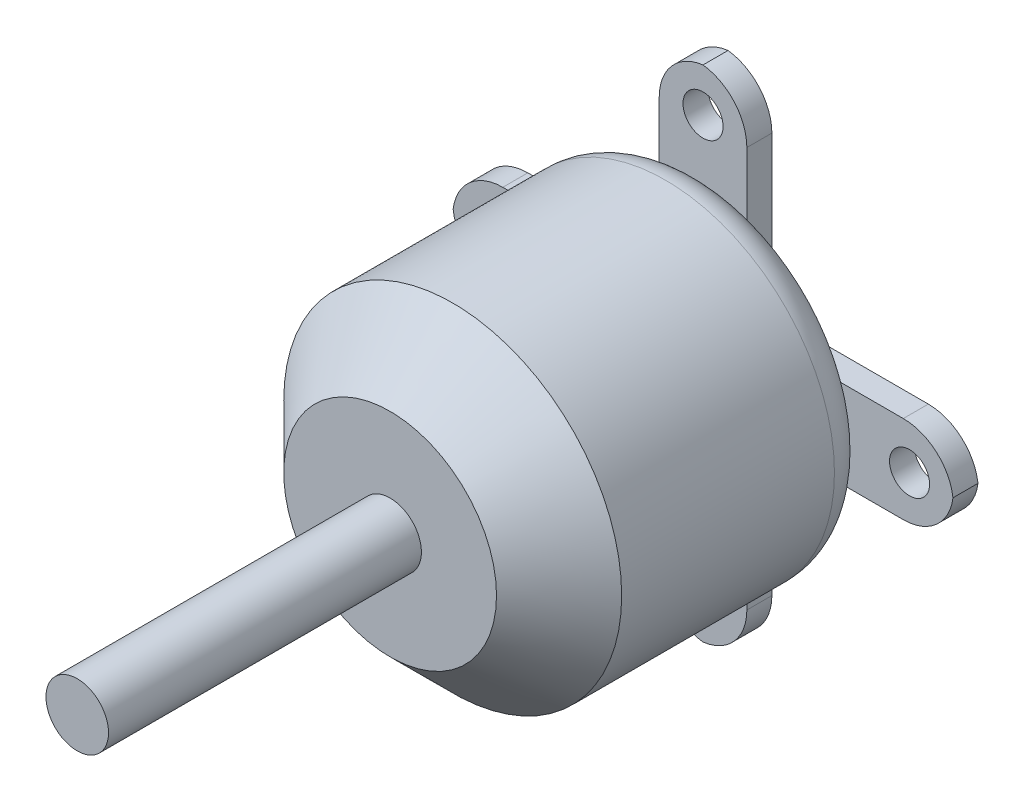
SolidWorks part; units mm, degrees
ref_plane "Front Plane" through (0, 0, 0) normal (0, 0, 1) x (1, 0, 0)
ref_plane "Top Plane" through (0, 0, 0) normal (0, 1, 0) x (1, 0, 0)
ref_plane "Right Plane" through (0, 0, 0) normal (1, 0, 0) x (0, 0, -1)
sketch "Sketch1" plane through (0, 0, 0) normal (0, 0, 1) x (1, 0, 0)
  circle A0 centre (0, 0) radius 13.5
extrude "Boss-Extrude1" add sketch "Sketch1" along normal blind 25
sketch "Sketch2" plane through (0, 0, 25) normal (0, 0, 1) x (1, 0, 0)
  circle A0 centre (0, 0) radius 2.5
extrude "Boss-Extrude2" add sketch "Sketch2" along normal blind 25
fillet "Fillet1" radius 3 1 edges at (13.5, 0, 0)
chamfer "Chamfer1" distance 5 angle 45 1 edges at (13.5, 0, 25)
sketch "Sketch3" plane through (0, 0, 0) normal (0, 0, -1) x (-1, 0, 0)
  line L0 (-3.5, -7.5) -> (-3.5, -16)
  line L1 (-16, 3.5) -> (-7.5, 3.5)
  line L3 (-16, -3.5) -> (-7.5, -3.5)
  line L6 (-3.5, 16) -> (-3.5, 7.5)
  line L8 (3.5, 16) -> (3.5, 7.5)
  line L9 (3.5, -7.5) -> (3.5, -16)
  line L10 (7.5, 3.5) -> (16, 3.5)
  line L11 (7.5, -3.5) -> (16, -3.5)
  arc A0 (3.5, 7.5) -> (7.5, 3.5) centre (7.5, 7.5) ccw
  arc A1 (3.5, -7.5) -> (7.5, -3.5) centre (7.5, -7.5) cw
  arc A2 (-3.5, -7.5) -> (-7.5, -3.5) centre (-7.5, -7.5) ccw
  arc A3 (-3.5, 7.5) -> (-7.5, 3.5) centre (-7.5, 7.5) cw
  circle A4 centre (-16.5, 0) radius 1.6
  arc A5 (-3.5, -16) -> (0, -19.9686) centre (0.5, -16) ccw
  arc A6 (0, -19.9686) -> (3.5, -16) centre (-0.5, -16) ccw
  arc A7 (16, -3.5) -> (19.9686, 0) centre (16, 0.5) ccw
  arc A8 (16, 3.5) -> (19.9686, 0) centre (16, -0.5) cw
  arc A9 (0, 19.9686) -> (3.5, 16) centre (-0.5, 16) cw
  arc A10 (0, 19.9686) -> (-3.5, 16) centre (0.5, 16) ccw
  arc A11 (-16, 3.5) -> (-19.9686, 0) centre (-16, -0.5) ccw
  arc A12 (-19.9686, 0) -> (-16, -3.5) centre (-16, 0.5) ccw
  circle A13 centre (0, 16.5) radius 1.6
  circle A14 centre (16.5, 0) radius 1.6
  circle A15 centre (0, -16.5) radius 1.6
  point P15 (3.5, 3.5)
  point P18 (3.5, -3.5)
  point P29 (3.5, -20)
  point P32 (20, -3.5)
  point P37 (3.5, 20)
  point P40 (-3.5, 20)
  point P43 (-20, 3.5)
  point P46 (-20, -3.5)
  point P56 (0, 0)
  dimension "D9" = 4
  dimension "D10" = 16.5
  dimension "D11" = 4
  dimension "D1" = 7
  dimension "D2" = 7
  dimension "D3" = 3.5
  dimension "D4" = 3.5
  dimension "D5" = 40
  dimension "D8" = 40
  dimension "D12" = 4
extrude "Boss-Extrude3" add sketch "Sketch3" along normal blind 2
sketch "Sketch4" plane through (0, 0, -2) normal (0, 0, -1) x (-1, 0, 0)
  circle A0 centre (0, 0) radius 4
extrude "Cut-Extrude1" cut sketch "Sketch4" against normal blind 2
